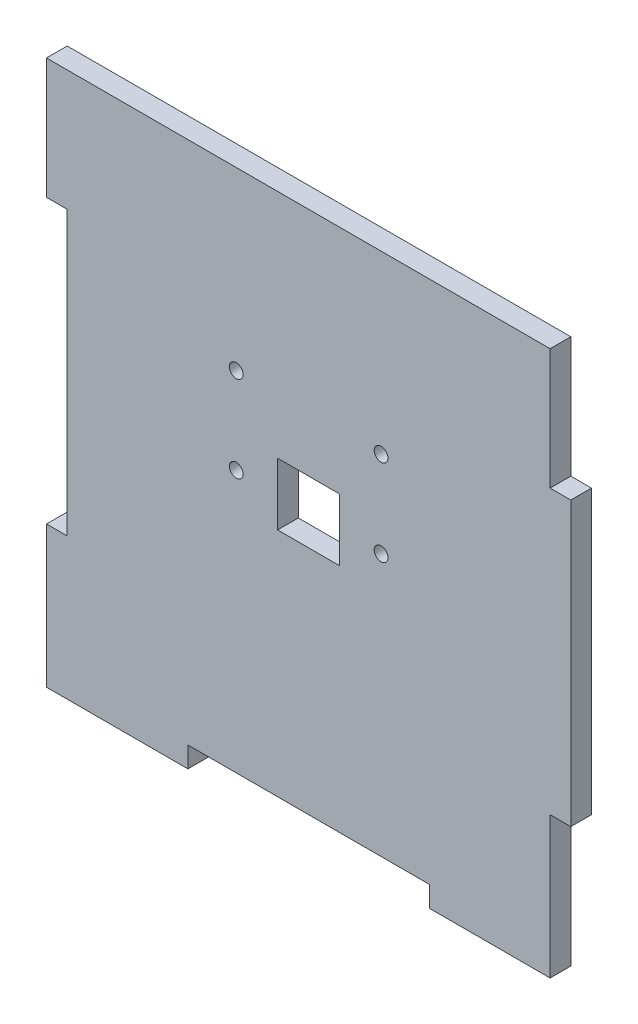
SolidWorks part; units mm, degrees
ref_plane "Front Plane" through (0, 0, 0) normal (0, 0, 1) x (1, 0, 0)
ref_plane "Top Plane" through (0, 0, 0) normal (0, 1, 0) x (1, 0, 0)
ref_plane "Right Plane" through (0, 0, 0) normal (1, 0, 0) x (0, 0, -1)
sketch "Sketch1" plane through (0, 0, 0) normal (0, 0, 1) x (1, 0, 0)
  line L0 (0, 35) -> (0, -38) construction
  line L5 (-35, 38) -> (-17.5, 38)
  line L6 (-35, 20.5) -> (-35, -20.5)
  line L7 (-17.5, -38) -> (17.5, -38)
  line L24 (35, 38) -> (35, 20.5)
  line L25 (-35, 38) -> (35, -38) construction
  line L26 (-35, -38) -> (35, 38) construction
  line L27 (-35, 0) -> (35, 0) construction
  line L31 (-35, -20.5) -> (-38, -20.5)
  line L32 (-35, 20.5) -> (-38, 20.5)
  line L33 (-38, 20.5) -> (-38, 38)
  line L34 (-38, 38) -> (-35, 38)
  line L35 (-38, -20.5) -> (-38, -38)
  line L36 (-17.5, 38) -> (17.5, 38)
  line L37 (35, -38) -> (35, -41)
  line L38 (35, -20.5) -> (38, -20.5)
  line L39 (35, -41) -> (17.5, -41)
  line L40 (35, 20.5) -> (38, 20.5)
  line L41 (17.5, -41) -> (17.5, -38)
  line L42 (-17.5, -38) -> (-17.5, -41)
  line L43 (38, 20.5) -> (38, -20.5)
  line L45 (-35, -41) -> (-17.5, -41)
  line L46 (17.5, 38) -> (35, 38)
  line L47 (35, -20.5) -> (35, -38)
  line L48 (-38, -38) -> (-38, -41)
  line L49 (-38, -41) -> (-35, -41)
  point P0 (0, 0)
  dimension "D1" = 76
  dimension "D2" = 70
  dimension "D3" = 17.5
  dimension "D4" = 17.5
  dimension "D5" = 3
  dimension "D6" = 3
  dimension "D7" = 3
extrude "Boss-Extrude1" add sketch "Sketch1" along normal blind 3
sketch "Sketch2" plane through (0, 0, 3) normal (0, 0, 1) x (1, 0, 0)
  line L0 (0, 14.5) -> (0, -9.5) construction
  line L1 (-4, -4) -> (4, -4) construction
  line L2 (-4, -4) -> (-4, 4) construction
  line L3 (-4, 4) -> (4, 4) construction
  line L4 (4, -4) -> (4, 4) construction
  line L5 (-4, -4) -> (4, 4) construction
  line L6 (-4, 4) -> (4, -4) construction
  line L11 (-12.5, -9.5) -> (12.5, -9.5) construction
  line L12 (-12.5, -9.5) -> (-12.5, 14.5) construction
  line L13 (-12.5, 14.5) -> (12.5, 14.5) construction
  line L14 (12.5, -9.5) -> (12.5, 14.5) construction
  line L15 (-12.5, -9.5) -> (12.5, 14.5) construction
  line L16 (-12.5, 14.5) -> (12.5, -9.5) construction
  line L18 (-4.5, -4.5) -> (4.5, -4.5)
  line L19 (-4.5, -4.5) -> (-4.5, 4.5)
  line L20 (-4.5, 4.5) -> (4.5, 4.5)
  line L21 (4.5, -4.5) -> (4.5, 4.5)
  line L22 (-4.5, -4.5) -> (4.5, 4.5) construction
  line L23 (-4.5, 4.5) -> (4.5, -4.5) construction
  circle A3 centre (-10.5, 12.5) radius 1
  circle A4 centre (-10.5, 0) radius 1
  circle A5 centre (10.5, 12.5) radius 1
  circle A6 centre (10.5, 0) radius 1
  point P0 (0, 0)
  point P6 (0, 0)
  point P7 (0, 2.5)
  point P19 (0, 0)
  dimension "D5" = 5.5
  dimension "D7" = 2
  dimension "D8" = 2
  dimension "D10" = 2
  dimension "D1" = 8
  dimension "D2" = 8
  dimension "D3" = 24
  dimension "D4" = 25
  dimension "D6" = 0
  dimension "D9" = 2
  dimension "D11" = 2
  dimension "D12" = 12.5
  dimension "D13" = 9
  dimension "D14" = 9
extrude "Cut-Extrude1" cut sketch "Sketch2" against normal blind 3
